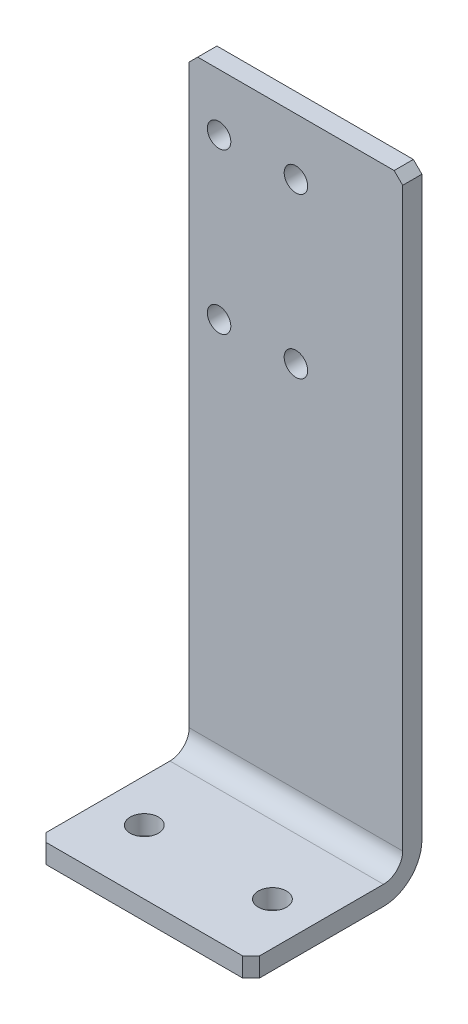
SolidWorks part; units mm, degrees
ref_plane "Front" through (0, 0, 0) normal (0, 0, 1) x (1, 0, 0)
ref_plane "Top" through (0, 0, 0) normal (0, 1, 0) x (1, 0, 0)
ref_plane "Right" through (0, 0, 0) normal (1, 0, 0) x (0, 0, -1)
sketch "Sketch1" plane through (0, 0, 0) normal (1, 0, 0) x (0, 0, -1)
  line L1 (0, 0) -> (-40, 0)
  line L2 (0, 0) -> (0, 146)
  line L3 (0, 146) -> (-4.5, 146)
  line L4 (-40, 0) -> (-40, 4.5)
  line L5 (-4.5, 4.5) -> (-40, 4.5)
  line L6 (-4.5, 4.5) -> (-4.5, 146)
  point P11 (0, 0)
  dimension "D1" = 4.5
  dimension "D2" = 4.5
  dimension "D3" = 40
  dimension "D4" = 146
extrude "Boss-Extrude1" add sketch "Sketch1" along normal mid plane 50
fillet "Fillet1" radius 4.5 1 edges at (0, 4.5, 4.5)
fillet "Fillet2" radius 9 1 edges at (0, 0, 0)
hole_wizard "M6 Clearance Hole1" positions "Sketch3" profile "Sketch2" hole size "M6" standard "JIS" end condition through all
sketch "Sketch3" plane through (0, 4.5, 0) normal (0, 1, 0) x (-1, 0, 0)
  line L1 (-25, 40) -> (25, 40) construction
  line L2 (0, 23.7031) -> (0, -2.2912) construction
  line L4 (-25, 9) -> (-25, 40) construction
  line L5 (25, 9) -> (25, 40) construction
  point P0 (15, 25)
  point P1 (-15, 25)
  dimension "D1" = 10
  dimension "D2" = 15
  dimension "D3" = 30
  dimension "D4" = 10
sketch "Sketch2" plane through (-15, 4.5, 25) normal (1, 0, 0) x (0, 0, 1)
  line L0 (0, 0) -> (0, 4.5)
  line L1 (0, 4.5) -> (3.3, 4.5)
  line L2 (3.3, 4.5) -> (3.3, 0)
  line L5 (3.3, 0) -> (0, 0)
  line L11 (0, -6.35) -> (0, 107.95) construction
  dimension "通し穴の直径" = 6.6
  dimension "通し穴の深さ" = 4.5
hole_wizard "M5 Clearance Hole1" positions "Sketch5" profile "Sketch4" hole size "M5" standard "JIS" end condition through all
sketch "Sketch5" plane through (0, 0, 0) normal (0, 0, -1) x (-1, 0, 0)
  line L8 (25, 9) -> (25, 146) construction
  line L9 (-25, 146) -> (25, 146) construction
  point P0 (18, 132.7)
  point P1 (0, 132.7)
  point P3 (0, 95.3)
  point P5 (18, 95.3)
  dimension "D1" = 37.4
  dimension "D2" = 18
  dimension "D3" = 7
  dimension "D4" = 13.3
sketch "Sketch4" plane through (-18, 132.7, 0) normal (1, 0, 0) x (0, 1, 0)
  line L0 (0, 0) -> (0, 40)
  line L1 (0, 40) -> (2.75, 40)
  line L2 (2.75, 40) -> (2.75, 0)
  line L5 (2.75, 0) -> (0, 0)
  line L11 (0, -6.35) -> (0, 107.95) construction
  dimension "通し穴の直径" = 5.5
  dimension "通し穴の深さ" = 40
chamfer "Chamfer1" distance 2 angle 45 4 edges at (-25, 2.25, 40) (25, 2.25, 40) (-25, 146, 2.25) (25, 146, 2.25)
